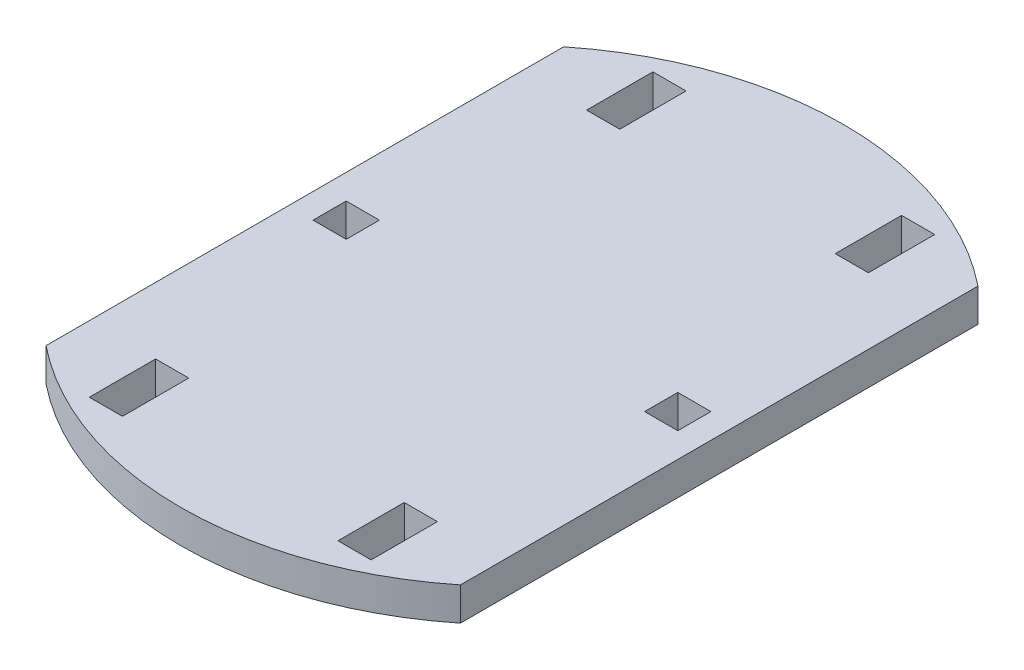
SolidWorks part; units mm, degrees
ref_plane "Front Plane" through (0, 0, 0) normal (0, 0, 1) x (1, 0, 0)
ref_plane "Top Plane" through (0, 0, 0) normal (0, 1, 0) x (1, 0, 0)
ref_plane "Right Plane" through (0, 0, 0) normal (1, 0, 0) x (0, 0, -1)
sketch "Sketch1" plane through (0, 0, 0) normal (0, 1, 0) x (1, 0, 0)
  line L0 (-25, 31.225) -> (-25, -31.225)
  line L1 (0, 0) -> (0, 40) construction
  line L2 (25, 31.225) -> (25, -31.225)
  line L3 (0, 0) -> (20, 0) construction
  line L4 (-18, -2) -> (-22, -2)
  line L5 (18, 2) -> (22, 2)
  line L6 (18, 2) -> (18, -2)
  line L7 (18, -2) -> (22, -2)
  line L8 (22, 2) -> (22, -2)
  line L9 (18, 2) -> (22, -2) construction
  line L10 (18, -2) -> (22, 2) construction
  line L11 (-22, 2) -> (-22, -2)
  line L12 (-18, 2) -> (-22, 2)
  line L13 (-18, 2) -> (-18, -2)
  line L35 (-9, 40) -> (9, 40) construction
  line L36 (-9, -20) -> (9, -20) construction
  line L37 (-9, -20) -> (-9, -40) construction
  line L38 (-9, -40) -> (9, -40) construction
  line L39 (9, -20) -> (9, -40) construction
  line L40 (9, 20) -> (9, 40) construction
  line L41 (-9, 20) -> (9, 20) construction
  line L42 (-9, 20) -> (-9, 40) construction
  line L43 (-13, 26) -> (-17, 26)
  line L44 (13, 34) -> (17, 34)
  line L45 (13, 34) -> (13, 26)
  line L46 (13, 26) -> (17, 26)
  line L47 (17, 34) -> (17, 26)
  line L48 (-17, 34) -> (-17, 26)
  line L49 (-13, 34) -> (-17, 34)
  line L50 (-13, 34) -> (-13, 26)
  line L51 (13, -26) -> (17, -26)
  line L52 (17, -34) -> (17, -26)
  line L53 (13, -34) -> (17, -34)
  line L54 (13, -34) -> (13, -26)
  line L55 (-13, -34) -> (-13, -26)
  line L56 (-13, -34) -> (-17, -34)
  line L57 (-17, -34) -> (-17, -26)
  line L58 (-13, -26) -> (-17, -26)
  circle A0 centre (0, 0) radius 40
  dimension "D1" = 80
  dimension "D2" = 18
  dimension "D3" = 4
  dimension "D4" = 20
  dimension "D5" = 20
  dimension "D6" = 50
  dimension "D7" = 16
  dimension "D8" = 6
  dimension "D9" = 4
  dimension "D10" = 4
  dimension "D11" = 8
extrude "Boss-Extrude1" add sketch "Sketch1" along normal blind 4
